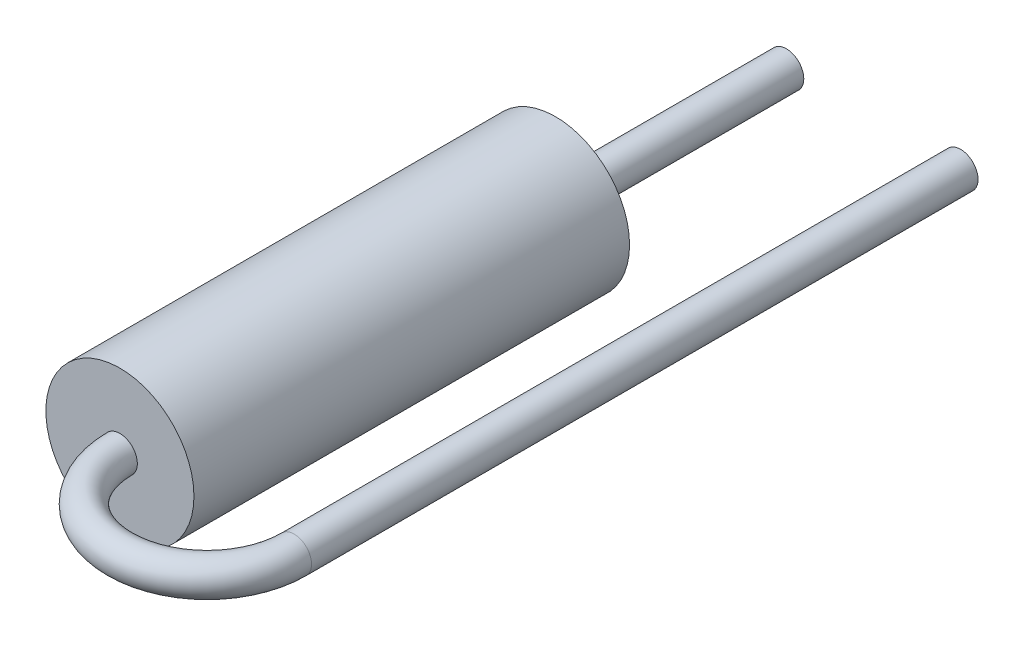
SolidWorks part; units mm, degrees
ref_plane "Front Plane" through (0, 0, 0) normal (0, 0, 1) x (1, 0, 0)
ref_plane "Top Plane" through (0, 0, 0) normal (0, 1, 0) x (1, 0, 0)
ref_plane "Right Plane" through (0, 0, 0) normal (1, 0, 0) x (0, 0, -1)
sketch "Sketch2" plane through (0, 0, 0) normal (0, 0, 1) x (1, 0, 0)
  circle A0 centre (0, 0) radius 1.7
  dimension "D1" = 3.4
extrude "Resistor Body" add sketch "Sketch2" along normal blind 10
sketch "Lead1 Path" plane through (0, 0, 0) normal (0, 1, 0) x (1, 0, 0)
  line L1 (0, -10) -> (0, 0) construction
  line L2 (-1.7, -10) -> (1.7, -10) construction
  line L4 (4, -10) -> (4, 5.3)
  arc A0 (4, -10) -> (0, -10) centre (2, -10) cw
  dimension "D1" = 4
  dimension "D2" = 15.3
sketch "Lead1 Profile" plane through (0, 0, 10) normal (0, 0, 1) x (-1, 0, 0)
  circle A0 centre (0, 0) radius 0.4
  dimension "D1" = 0.8
sweep "Lead1" add profiles "Lead1 Profile" path "Lead1 Path"
sketch "Sketch6" plane through (0, 0, 0) normal (0, 0, -1) x (1, 0, 0)
  circle A0 centre (0, 0) radius 0.4 construction
  circle A2 centre (0, 0) radius 0.4
extrude "Lead2" add sketch "Sketch6" along normal up to surface (5.3 mm away) up to face at (3.6, 0, -5.3)
ref_plane "Insertion plane" through (0, 0, -2) normal (0, 0, 1) x (1, 0, 0)
sketch "Component_Outline" plane through (0, 0, -2) normal (0, 0, 1) x (1, 0, 0)
  line L0 (1.6523, 0.4) -> (4, 0.4)
  line L1 (4, 0.4) -> (0, 0.4) construction
  line L2 (4, -0.4) -> (1.6523, -0.4)
  line L3 (0, -0.4) -> (4, -0.4) construction
  arc A0 (1.6523, 0.4) -> (1.6523, -0.4) centre (0, 0) ccw
  arc A1 (4, 0.4) -> (4, -0.4) centre (4, 0) cw
  circle A2 centre (4, 0) radius 0.4 construction
  dimension "D1" = 1.7
